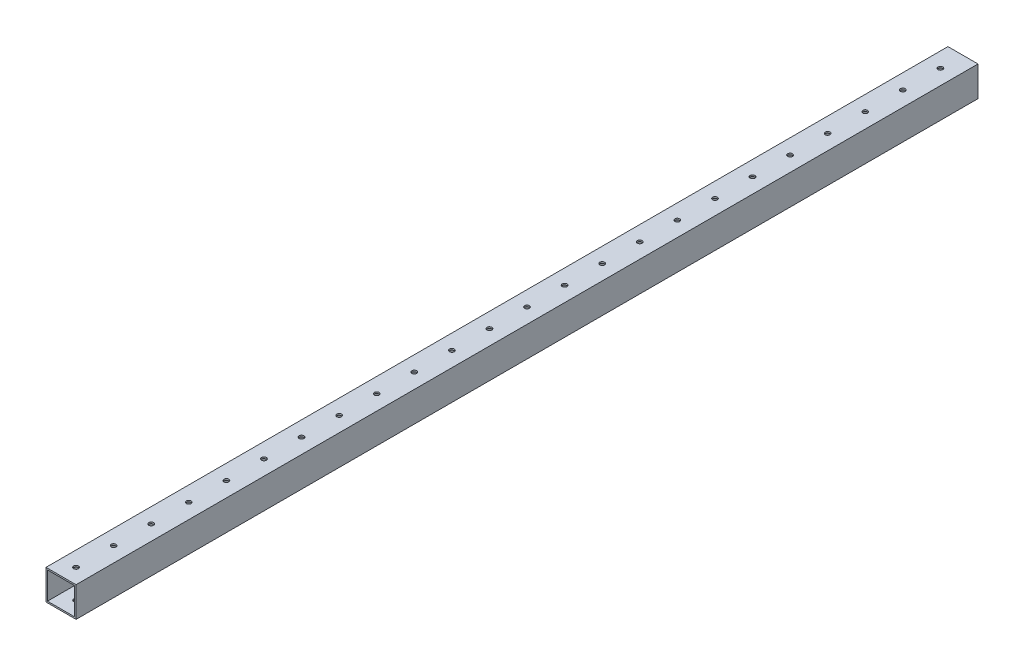
SolidWorks part; units mm, degrees
material "1060 合金"
ref_plane "前视基准面" through (0, 0, 0) normal (0, 0, 1) x (1, 0, 0)
ref_plane "上视基准面" through (0, 0, 0) normal (0, 1, 0) x (1, 0, 0)
ref_plane "右视基准面" through (0, 0, 0) normal (1, 0, 0) x (0, 0, -1)
other "Configuration Table"
sketch "草图1" plane through (0, 0, 0) normal (0, 0, 1) x (1, 0, 0)
  line L1 (10, -10) -> (10, 10)
  line L2 (10, 10) -> (-10, 10)
  line L3 (-10, 10) -> (-10, -10)
  line L4 (-10, -10) -> (10, -10)
  line L5 (9, -9) -> (9, 9)
  line L6 (9, 9) -> (-9, 9)
  line L7 (-9, 9) -> (-9, -9)
  line L8 (-9, -9) -> (9, -9)
  circle A0 centre (0, 0) radius 10 construction
  circle A1 centre (0, 0) radius 9 construction
  dimension "D1" = 20
  dimension "D2" = 18
extrude "凸台-拉伸1" add sketch "草图1" along normal blind 600
sketch "草图2" plane through (0, 10, 0) normal (0, 1, 0) x (1, 0, 0)
  line L0 (0, -15) -> (0, -40) construction
  circle A0 centre (0, -15) radius 1.6
  circle A1 centre (0, -40) radius 1.6
  circle A2 centre (0, -65) radius 1.6
  circle A3 centre (0, -90) radius 1.6
  circle A4 centre (0, -115) radius 1.6
  circle A5 centre (0, -140) radius 1.6
  circle A6 centre (0, -165) radius 1.6
  circle A7 centre (0, -190) radius 1.6
  circle A8 centre (0, -215) radius 1.6
  circle A9 centre (0, -240) radius 1.6
  circle A10 centre (0, -265) radius 1.6
  circle A11 centre (0, -290) radius 1.6
  circle A12 centre (0, -315) radius 1.6
  circle A13 centre (0, -340) radius 1.6
  circle A14 centre (0, -365) radius 1.6
  circle A15 centre (0, -390) radius 1.6
  circle A16 centre (0, -415) radius 1.6
  circle A17 centre (0, -440) radius 1.6
  circle A18 centre (0, -465) radius 1.6
  circle A19 centre (0, -490) radius 1.6
  circle A20 centre (0, -515) radius 1.6
  circle A21 centre (0, -540) radius 1.6
  circle A22 centre (0, -565) radius 1.6
  circle A23 centre (0, -590) radius 1.6
  dimension "D1" = 3.2
  dimension "D2" = 13.4
  dimension "D4" = 25
  dimension "D3" = 24
extrude "切除-拉伸1" cut sketch "草图2" against normal through all
